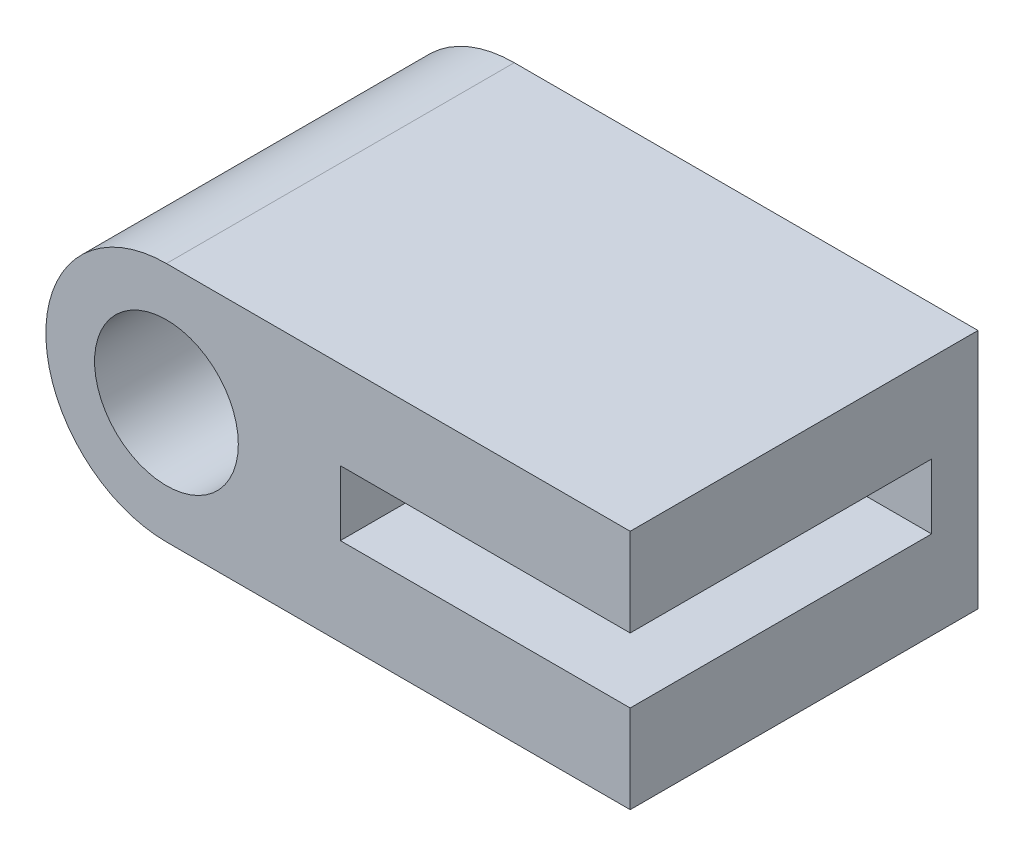
SolidWorks part; units mm, degrees
ref_plane "Alzado" through (0, 0, 0) normal (0, 0, 1) x (1, 0, 0)
ref_plane "Planta" through (0, 0, 0) normal (0, 1, 0) x (1, 0, 0)
ref_plane "Vista lateral" through (0, 0, 0) normal (1, 0, 0) x (0, 0, -1)
sketch "Croquis1" plane through (0, 0, 0) normal (0, 0, 1) x (1, 0, 0)
  line L0 (0, 5.2) -> (20, 5.2)
  line L1 (20, 5.2) -> (20, -5.2)
  line L2 (20, -5.2) -> (0, -5.2)
  circle A0 centre (0, 0) radius 3.1
  arc A1 (0, 5.2) -> (0, -5.2) centre (0, 0) ccw
  dimension "D1" = 6.2
  dimension "D2" = 10.4
  dimension "D3" = 20
extrude "Saliente-Extruir1" add sketch "Croquis1" along normal blind 15
sketch "Croquis2" plane through (0, 0, 15) normal (0, 0, 1) x (1, 0, 0)
  line L0 (20, -5.2) -> (20, 5.2) construction
  line L1 (20, -1.4) -> (7.5, -1.4)
  line L2 (20, -1.4) -> (20, 1.4)
  line L3 (20, 1.4) -> (7.5, 1.4)
  line L4 (7.5, -1.4) -> (7.5, 1.4)
  point P6 (20, 0)
  point P7 (20, 0)
  dimension "D1" = 7.5
  dimension "D2" = 2.8
extrude "Cortar-Extruir1" cut sketch "Croquis2" against normal offset from surface (13 mm away) 2 up to face at (8.7, 0, 0)
